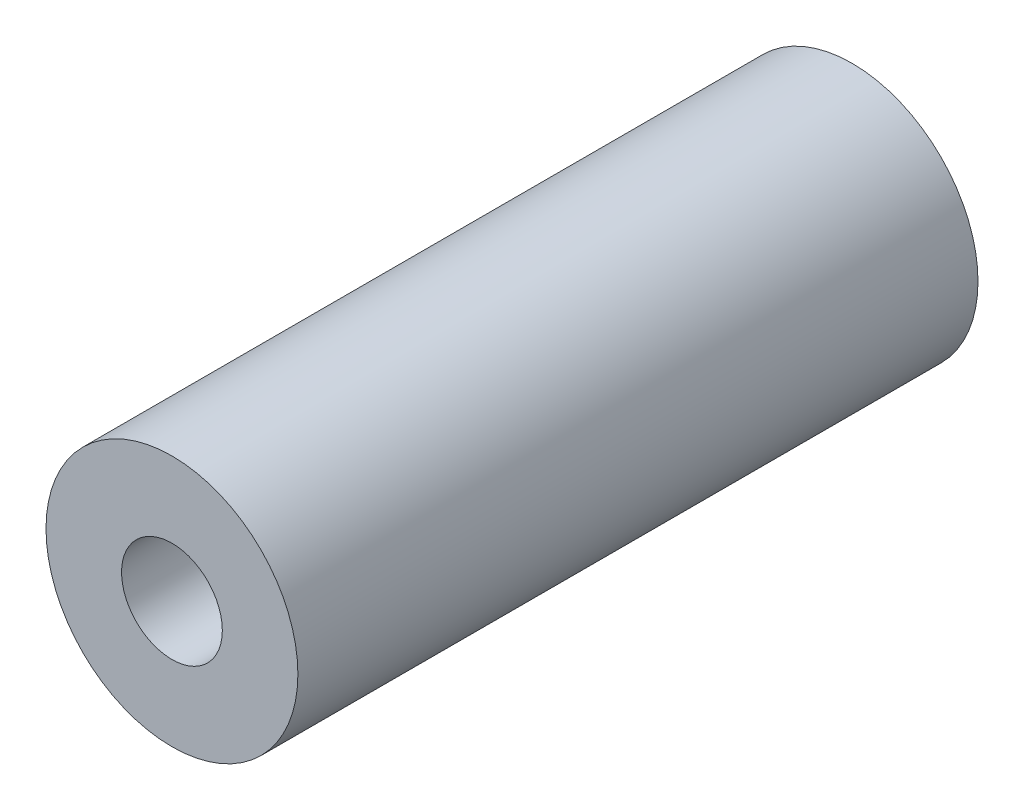
SolidWorks part; units mm, degrees
ref_plane "前视基准面" through (0, 0, 0) normal (0, 0, 1) x (1, 0, 0)
ref_plane "上视基准面" through (0, 0, 0) normal (0, 1, 0) x (1, 0, 0)
ref_plane "右视基准面" through (0, 0, 0) normal (1, 0, 0) x (0, 0, -1)
sketch "草图1" plane through (0, 0, 0) normal (0, 0, 1) x (1, 0, 0)
  circle A0 centre (0, 0) radius 10
  dimension "D1" = 20
extrude "凸台-拉伸1" add sketch "草图1" along normal blind 54
sketch "草图2" plane through (0, 0, 54) normal (0, 0, 1) x (1, 0, 0)
  circle A0 centre (0, 0) radius 4
  dimension "D1" = 8
extrude "切除-拉伸1" cut sketch "草图2" against normal through all
